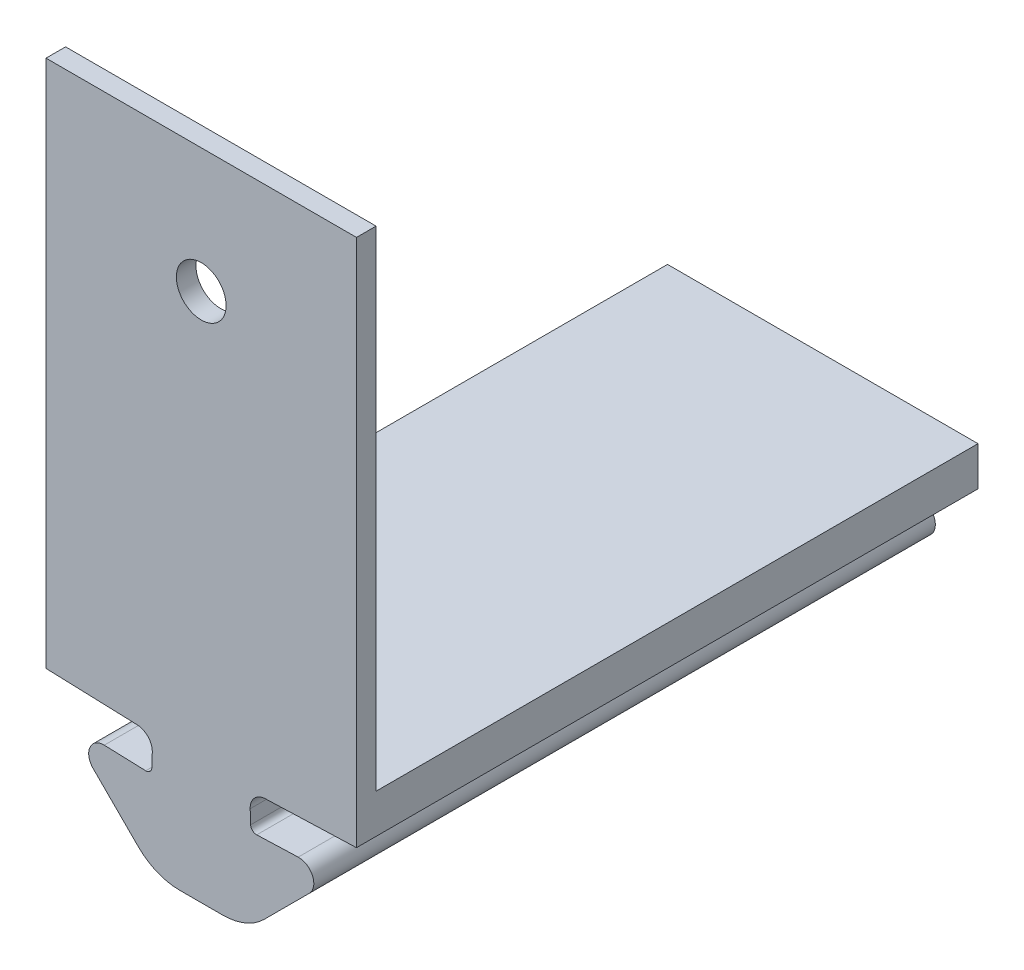
SolidWorks part; units mm, degrees
ref_plane "Front Plane" through (0, 0, 0) normal (0, 0, 1) x (1, 0, 0)
ref_plane "Top Plane" through (0, 0, 0) normal (0, 1, 0) x (1, 0, 0)
ref_plane "Right Plane" through (0, 0, 0) normal (1, 0, 0) x (0, 0, -1)
sketch "Sketch2" plane through (0, 0, 0) normal (0, 0, 1) x (1, 0, 0)
  line L1 (-50.3756, 45.6099) -> (-50.3512, 46.3094)
  line L2 (-50.6859, 45.3205) -> (-52.8037, 45.3945)
  line L6 (-55.7809, 47.2995) -> (-51.1228, 47.1369)
  line L7 (-51.0743, 41.7794) -> (-53.3751, 44.0803)
  line L8 (-47.8507, 40.9008) -> (-48.9529, 40.9008)
  line L9 (-47.8507, 40.9008) -> (-47.8507, 47.2995)
  line L10 (-47.8507, 47.2995) -> (-55.7809, 47.2995)
  arc A0 (-50.6859, 45.3205) -> (-50.3756, 45.6099) centre (-50.6754, 45.6203) ccw
  arc A7 (-50.3512, 46.3094) -> (-51.1228, 47.1369) centre (-51.1507, 46.3374) ccw
  arc A8 (-52.8037, 45.3945) -> (-53.3751, 44.0803) centre (-52.8306, 44.6248) ccw
  arc A9 (-51.0743, 41.7794) -> (-48.9529, 40.9008) centre (-48.9529, 43.9008) ccw
extrude "Boss-Extrude1" add sketch "Sketch2" along normal blind 31.75
ref_plane "Plane2" through (0, 0, 0) normal (0.7071, -0.7071, 0) x (-0.7071, -0.7071, 0)
ref_plane "Plane3" through (-42.746, 42.746, 0) normal (0.7071, -0.7071, 0) x (-0.7071, -0.7071, 0)
mirror "Mirror2" about plane through (-47.8507, 40.9008, 31.75) normal (-1, 0, 0) of "Boss-Extrude1"
ref_plane "Plane7" through (0, 47.2995, 0) normal (0, 1, 0) x (1, 0, 0)
sketch "Sketch19" plane through (0, 47.2995, 0) normal (0, 1, 0) x (1, 0, 0)
  line L0 (-55.7809, -31.75) -> (-55.7809, 0) construction
  line L1 (-55.7809, 0) -> (-39.9205, 0)
  line L2 (-55.7809, 0) -> (-55.7809, -31.75)
  line L3 (-55.7809, -31.75) -> (-39.9205, -31.75)
  line L4 (-39.9205, 0) -> (-39.9205, -31.75)
  line L5 (-39.9205, -31.75) -> (-39.9205, 0) construction
  line L6 (-39.9205, 0) -> (-55.7809, 0) construction
  dimension "D1" = 0
  dimension "D2" = 31.75
extrude "Boss-Extrude7" add sketch "Sketch19" along normal blind 2
sketch "Sketch23" plane through (0, 49.2995, 0) normal (0, 1, 0) x (1, 0, 0)
  line L0 (-55.7809, 0) -> (-55.7809, -31.75) construction
  line L1 (-55.7809, -30.75) -> (-39.9205, -30.75)
  line L2 (-55.7809, -30.75) -> (-55.7809, -31.75)
  line L3 (-55.7809, -31.75) -> (-39.9205, -31.75)
  line L4 (-39.9205, -30.75) -> (-39.9205, -31.75)
  line L5 (-39.9205, -31.75) -> (-39.9205, 0) construction
  line L8 (-55.7809, -31.75) -> (-39.9205, -31.75) construction
  dimension "D1" = 0
  dimension "D2" = 0
  dimension "D3" = 0
  dimension "D4" = 1
extrude "Boss-Extrude8" add sketch "Sketch23" along normal blind 25
ref_plane "Plane8" through (-39.9205, 49.2995, 30.75) normal (0, -1, 0) x (-1, 0, 0)
sketch "Sketch24" plane through (0, 0, 30.75) normal (0, 0, -1) x (-1, 0, 0)
  line L0 (39.9205, 74.2995) -> (55.7809, 74.2995) construction
  line L5 (47.8507, 74.2995) -> (47.8507, 61.5995) construction
  circle A1 centre (47.8507, 67.9495) radius 1.27
  dimension "D1" = 6.35
  dimension "D4" = 2.54
extrude "Cut-Extrude1" cut sketch "Sketch24" against normal blind 2.54
